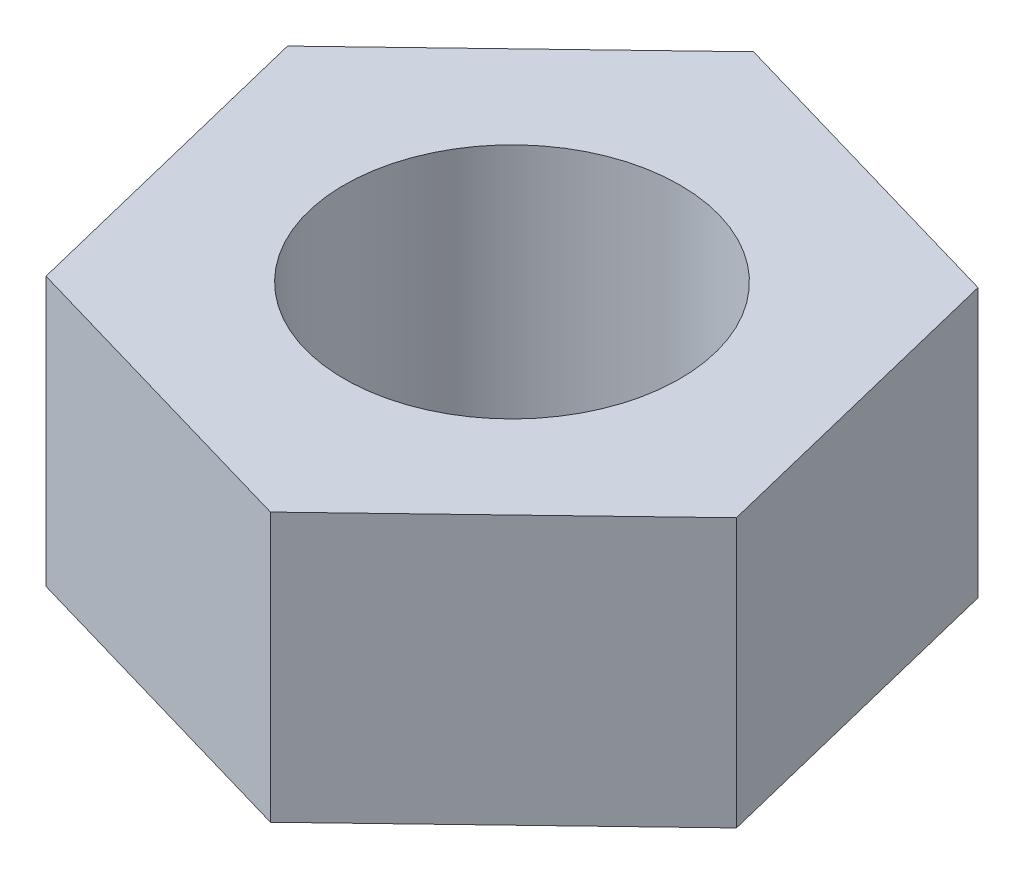
SolidWorks part; units mm, degrees
ref_plane "Płaszczyzna XY" through (0, 0, 0) normal (0, 0, 1) x (1, 0, 0)
ref_plane "Płaszczyzna XZ" through (0, 0, 0) normal (0, 1, 0) x (1, 0, 0)
ref_plane "Płaszczyzna YZ" through (0, 0, 0) normal (1, 0, 0) x (0, 0, -1)
sketch "Szkic1" plane through (0, 0, 0) normal (0, 1, 0) x (1, 0, 0)
  line L1 (-2.3388, 9.5322) -> (-9.4245, 2.7407)
  line L2 (-9.4245, 2.7407) -> (-7.0858, -6.7915)
  line L3 (-7.0858, -6.7915) -> (2.3388, -9.5322)
  line L4 (2.3388, -9.5322) -> (9.4245, -2.7407)
  line L5 (9.4245, -2.7407) -> (7.0858, 6.7915)
  line L6 (7.0858, 6.7915) -> (-2.3388, 9.5322)
  circle A0 centre (0, 0) radius 8.5 construction
  dimension "D1" = 17
extrude "Dodanie-wyciągnięcie1" add sketch "Szkic1" along normal blind 8
sketch "Szkic2" plane through (0, 0, 0) normal (0, -1, 0) x (-1, 0, 0)
  circle A0 centre (0, 0) radius 5
  dimension "D1" = 10
extrude "Wytnij-wyciągnięcie1" cut sketch "Szkic2" against normal through all
